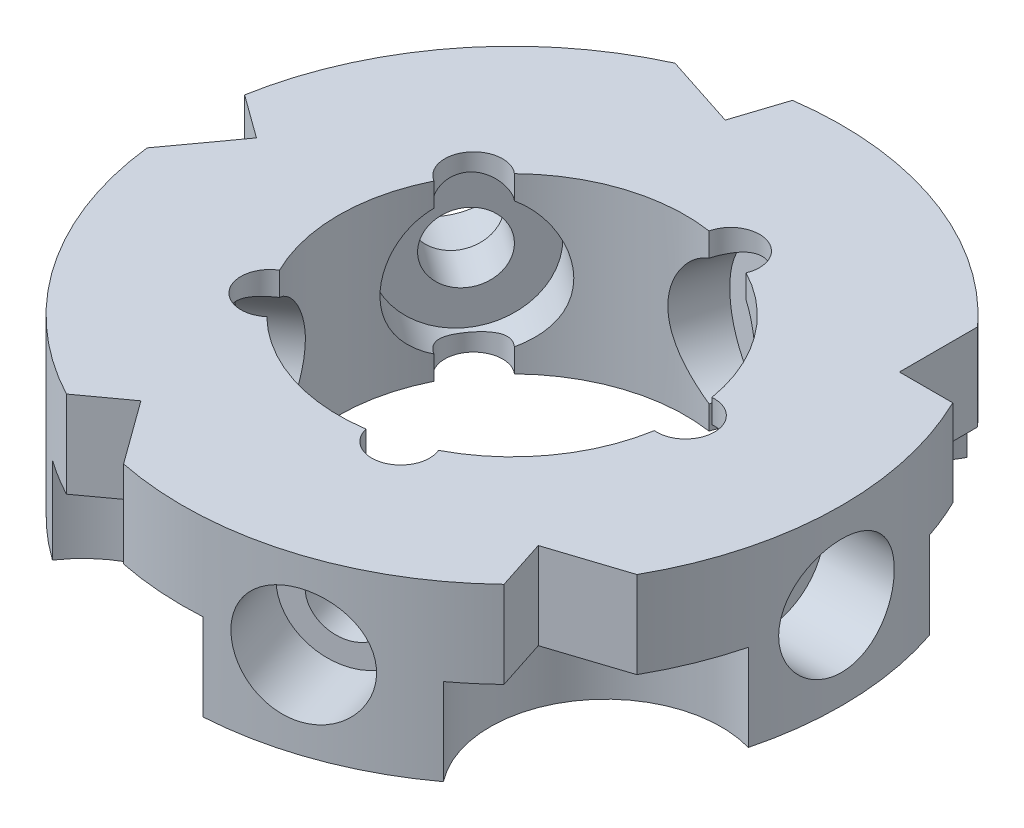
SolidWorks part; units mm, degrees
material "Alloy Steel"
ref_plane "Front Plane" through (0, 0, 0) normal (0, 0, 1) x (1, 0, 0)
ref_plane "Top Plane" through (0, 0, 0) normal (0, 1, 0) x (1, 0, 0)
ref_plane "Right Plane" through (0, 0, 0) normal (1, 0, 0) x (0, 0, -1)
sketch "Sketch1" plane through (0, 0, 0) normal (0, 1, 0) x (1, 0, 0)
  circle A0 centre (0, 0) radius 28.5
  circle A1 centre (0, 0) radius 15
  dimension "D1" = 57
  dimension "D2" = 30
extrude "Boss-Extrude1" add sketch "Sketch1" along normal mid plane 15
sketch "Sketch3" plane through (0, 0, 0) normal (0, 0, 1) x (1, 0, 0)
  line L0 (0, 0) -> (38.6034, 0) construction
  line L1 (0, 0) -> (0, 6)
  line L2 (0, 6) -> (18, 6)
  line L3 (18, 6) -> (18, 3)
  line L4 (18, 3) -> (22, 3)
  line L5 (22, 3) -> (22, 5)
  line L6 (22, 5) -> (28.5, 5)
  line L7 (28.5, 5) -> (28.5, 0)
  line L8 (28.5, 0) -> (0, 0)
  line L9 (28.5, -7.5) -> (28.5, 7.5) construction
  dimension "D1" = 12
  dimension "D2" = 6
  dimension "D3" = 10
  dimension "D4" = 18
  dimension "D5" = 22
revolve "Cut-Revolve1" cut sketch "Sketch3" angle 360 about L0
sketch "Sketch4" plane through (0, 0, 0) normal (0, 1, 0) x (1, 0, 0)
  line L0 (0, 0) -> (37.3116, 0) construction
  line L1 (0, 0) -> (29.5383, 17.5823) construction
  line L2 (21, 19.2678) -> (21, 12.5)
  line L3 (21, 12.5) -> (25.6125, 12.5)
  circle A0 centre (0, 0) radius 28.5 construction
  arc A1 (21, 19.2678) -> (25.6125, 12.5) centre (0, 0) cw
  dimension "D1" = 12.5
  dimension "D2" = 21
extrude "Cut-Extrude1" cut sketch "Sketch4" against normal through all both and the other way through all
sketch "Sketch5" plane through (0, 0, 0) normal (0, 1, 0) x (1, 0, 0)
  circle A0 centre (15, 0) radius 2.5
  arc A1 (13.7477, -6) -> (13.7477, 6) centre (0, 0) ccw construction
  dimension "D1" = 5
extrude "Cut-Extrude2" cut sketch "Sketch5" against normal through all both and the other way through all
sketch "Sketch6" plane through (0, -7.5, 0) normal (0, -1, 0) x (1, 0, 0)
  line L0 (0, 0) -> (23.6403, -18.4698) construction
  line L1 (0, 0) -> (35.3081, 0) construction
  arc A0 (27.0219, -9.059) -> (15.3271, -24.0277) centre (23.6403, -18.4698) ccw
  arc A1 (15.3271, -24.0277) -> (27.0219, -9.059) centre (0, 0) ccw
  arc A2 (25.6125, -12.5) -> (21, -19.2678) centre (0, 0) ccw construction
  dimension "D1" = 10
  dimension "D2" = 30
  dimension "D3" = 38
extrude "Cut-Extrude4" cut sketch "Sketch6" against normal blind 7.5
pattern_circular "CirPattern1" count 5 over 360 about axis through (0, 0, 0) along (0, 1, 0) of "Cut-Revolve1", "Cut-Extrude1", "Cut-Extrude2", "Cut-Extrude4"
